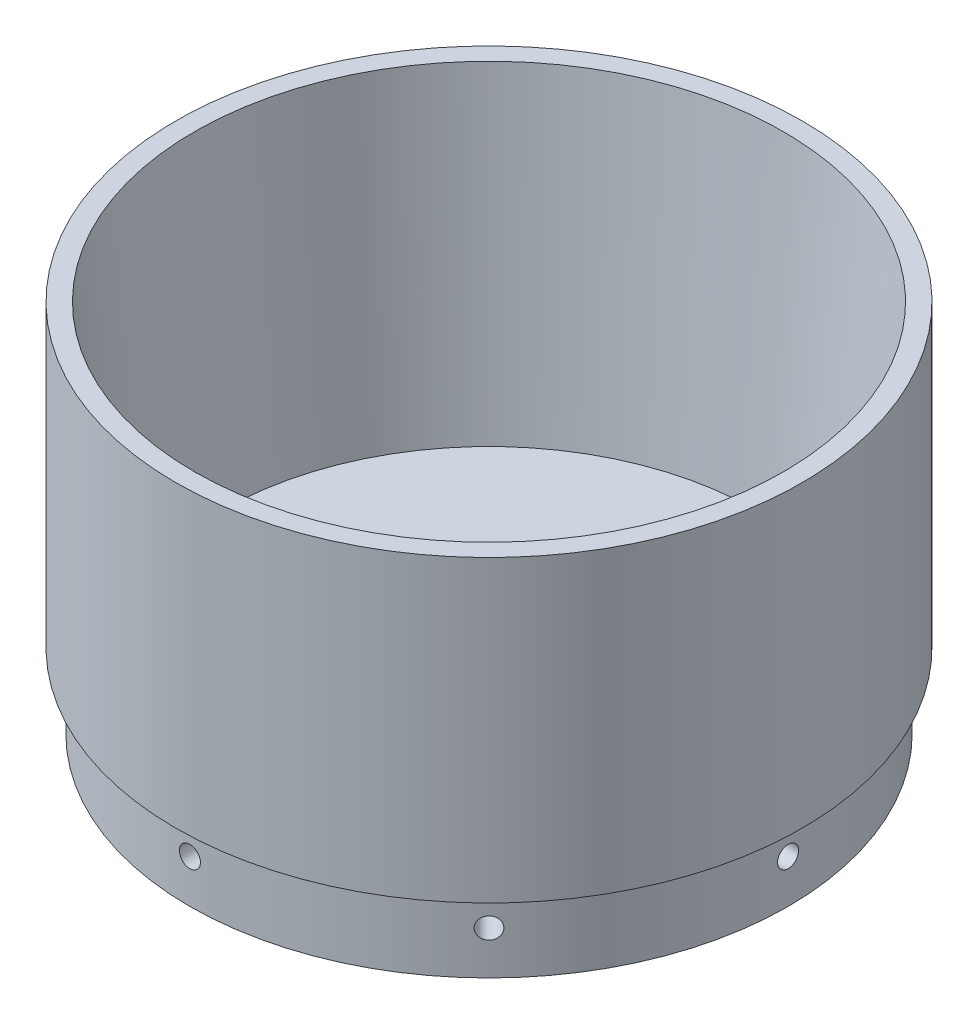
SolidWorks part; units mm, degrees
ref_plane "Front Plane" through (0, 0, 0) normal (0, 0, 1) x (1, 0, 0)
ref_plane "Top Plane" through (0, 0, 0) normal (0, 1, 0) x (1, 0, 0)
ref_plane "Right Plane" through (0, 0, 0) normal (1, 0, 0) x (0, 0, -1)
sketch "Sketch1" plane through (0, 0, 0) normal (0, 1, 0) x (1, 0, 0)
  circle A0 centre (0, 0) radius 53.1812
  dimension "D1" = 106.3625
extrude "Boss-Extrude1" add sketch "Sketch1" along normal blind 50.8
sketch "Sketch2" plane through (0, 0, 0) normal (0, -1, 0) x (1, 0, 0)
  circle A0 centre (0, 0) radius 50.8
  circle A1 centre (0, 0) radius 47.625
  dimension "D1" = 101.6
  dimension "D2" = 95.25
extrude "Boss-Extrude2" add sketch "Sketch2" along normal blind 12.7 contours A1 | A0 A1
sketch "Sketch3" plane through (0, 50.8, 0) normal (0, 1, 0) x (1, 0, 0)
  circle A0 centre (0, 0) radius 50.0062
  dimension "D1" = 100.0125
extrude "Cut-Extrude1" cut sketch "Sketch3" against normal offset from surface 10.16 draft 5 contours A0
sketch "Sketch4" plane through (0, -2.54, 0) normal (0, 1, 0) x (1, 0, 0)
  circle A1 centre (0, 0) radius 45.3396
  circle A8 centre (0, 0) radius 3.302
  circle A10 centre (0, 0) radius 45.3396
  dimension "D2" = 6.604
  dimension "D1" = 0
extrude "Cut-Extrude2" cut sketch "Sketch4" against normal through all contours A8
ref_plane "Plane1" through (50.8, 0, 0) normal (1, 0, 0) x (0, 0, -1)
sketch "Sketch5" plane through (50.8, 0, 0) normal (1, 0, 0) x (0, 0, -1)
  line L0 (0, 0) -> (0, -13.5799) construction
  line L1 (-50.8, 0) -> (50.8, 0) construction
  circle A0 centre (0, -5.353) radius 1.7859
  dimension "D1" = 3.5719
  dimension "D2" = 5.353
extrude "Cut-Extrude3" cut sketch "Sketch5" against normal blind 10.16
pattern_circular "CirPattern1" count 8 over 360 about axis through (0, 0, 0) along (0, 1, 0) of "Cut-Extrude3"
